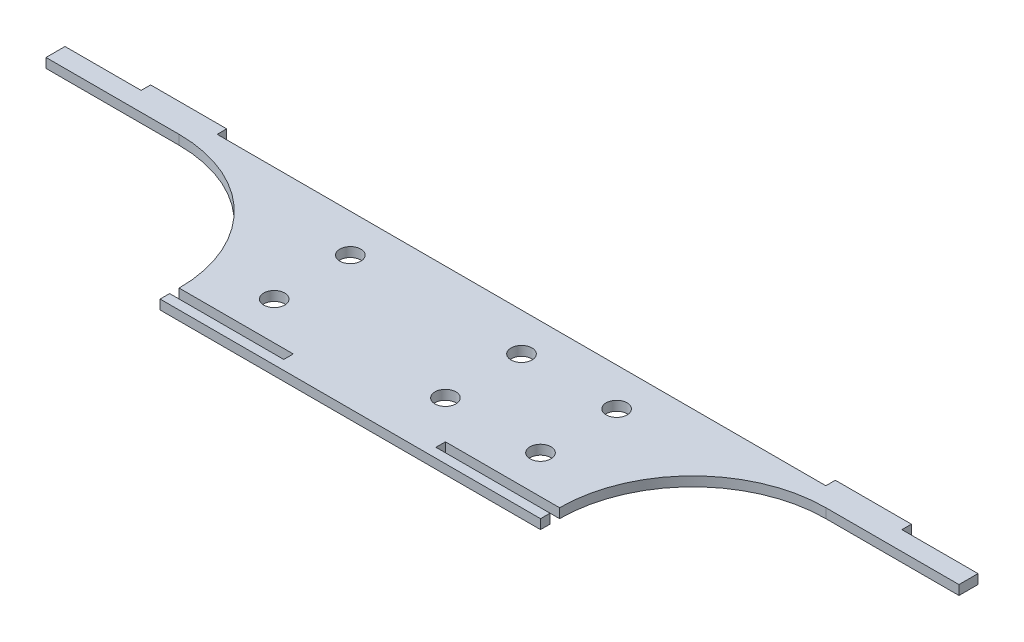
SolidWorks part; units mm, degrees
ref_plane "Front Plane" through (0, 0, 0) normal (0, 0, 1) x (1, 0, 0)
ref_plane "Top Plane" through (0, 0, 0) normal (0, 1, 0) x (1, 0, 0)
ref_plane "Right Plane" through (0, 0, 0) normal (1, 0, 0) x (0, 0, -1)
sketch "Sketch1" plane through (0, 0, 0) normal (0, 1, 0) x (1, 0, 0)
  line L0 (-107.95, 19.05) -> (-152.4, 19.05)
  line L1 (-152.4, -25.4) -> (152.4, -25.4)
  line L2 (-152.4, -25.4) -> (-152.4, 25.4)
  line L3 (-152.4, 25.4) -> (152.4, 25.4)
  line L4 (152.4, -25.4) -> (152.4, 25.4)
  line L5 (-152.4, -25.4) -> (152.4, 25.4) construction
  line L6 (-152.4, 25.4) -> (152.4, -25.4) construction
  line L7 (152.4, 19.05) -> (107.95, 19.05)
  line L8 (44.45, 12.7) -> (12.7, 12.7) construction
  line L9 (-44.45, -12.7) -> (44.45, -12.7) construction
  line L10 (-44.45, -12.7) -> (-44.45, 12.7) construction
  line L11 (-44.45, 12.7) -> (44.45, 12.7) construction
  line L12 (44.45, -12.7) -> (44.45, 12.7) construction
  line L13 (-44.45, -12.7) -> (44.45, 12.7) construction
  line L14 (-44.45, 12.7) -> (44.45, -12.7) construction
  line L15 (127, 28.575) -> (152.4, 28.575) construction
  line L16 (-25.4, -25.4) -> (25.4, -25.4)
  line L17 (-25.4, -25.4) -> (-25.4, -28.575)
  line L18 (-25.4, -28.575) -> (25.4, -28.575)
  line L19 (25.4, -25.4) -> (25.4, -28.575)
  line L20 (-127, 28.575) -> (-101.6, 28.575)
  line L21 (-127, 28.575) -> (-127, 25.4)
  line L22 (-127, 25.4) -> (-101.6, 25.4)
  line L23 (-101.6, 28.575) -> (-101.6, 25.4)
  line L24 (101.6, 28.575) -> (127, 28.575)
  line L25 (101.6, 28.575) -> (101.6, 25.4)
  line L26 (101.6, 25.4) -> (127, 25.4)
  line L27 (127, 28.575) -> (127, 25.4)
  line L28 (-127, 28.575) -> (-152.4, 28.575) construction
  line L30 (-63.5, -31.75) -> (63.5, -31.75)
  line L31 (-63.5, -31.75) -> (-63.5, -28.575)
  line L32 (-63.5, -28.575) -> (63.5, -28.575)
  line L33 (63.5, -31.75) -> (63.5, -28.575)
  arc A0 (-107.95, 19.05) -> (-63.5, -25.4) centre (-107.95, -25.4) cw
  arc A1 (107.95, 19.05) -> (63.5, -25.4) centre (107.95, -25.4) ccw
  circle A2 centre (-44.45, 12.7) radius 3.5
  circle A3 centre (-44.45, -12.7) radius 3.5
  circle A4 centre (44.45, 12.7) radius 3.5
  circle A5 centre (44.45, -12.7) radius 3.5
  circle A6 centre (12.7, 12.7) radius 3.5
  circle A7 centre (12.7, -12.7) radius 3.5
  point P0 (0, 0)
  point P14 (0, 0)
  point P31 (0, -28.575)
  point P46 (0, 0)
  dimension "D4" = 44.45
  dimension "D8" = 7
  dimension "D9" = 7
  dimension "D1" = 50.8
  dimension "D2" = 304.8
  dimension "D3" = 44.45
  dimension "D5" = 88.9
  dimension "D6" = 25.4
  dimension "D7" = 31.75
  dimension "D10" = 3.175
  dimension "D11" = 50.8
  dimension "D12" = 25.4
  dimension "D13" = 3.175
extrude "Boss-Extrude1" add sketch "Sketch1" along normal blind 3.175 contours L0 A0 L1 L4 L3 L2 | L30 L33 L32 L18 L31 | L21 L20 L23 L22 | L25 L24 L27 L26
